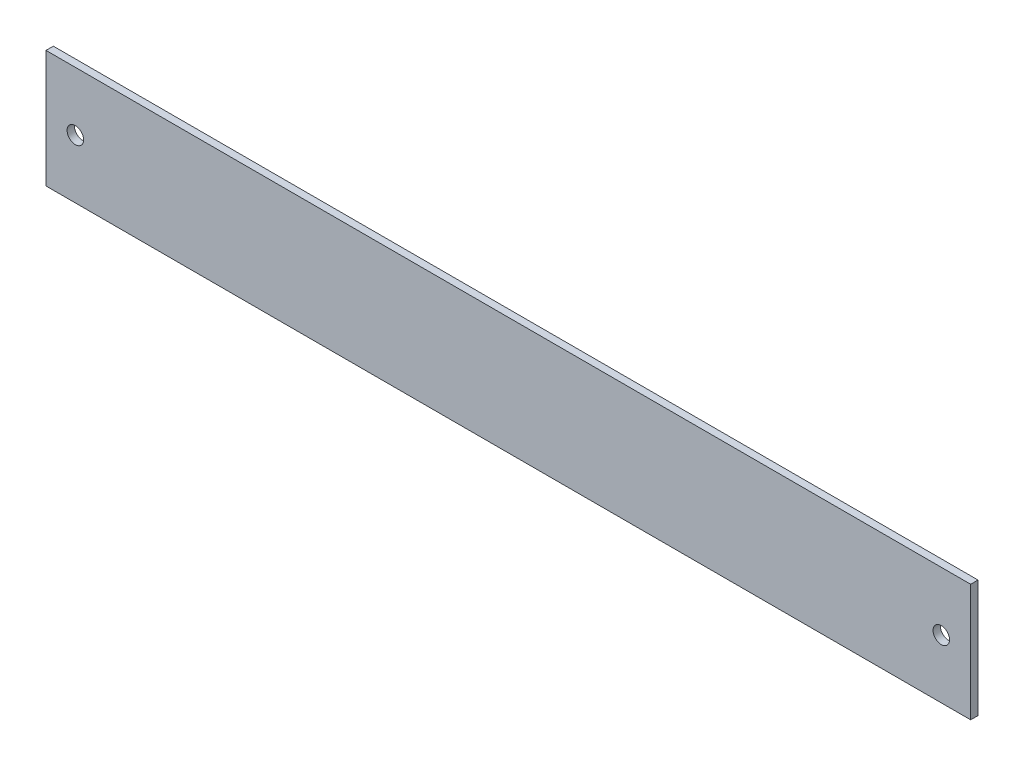
SolidWorks part; units mm, degrees
ref_plane "Front Plane" through (0, 0, 0) normal (0, 0, 1) x (1, 0, 0)
ref_plane "Top Plane" through (0, 0, 0) normal (0, 1, 0) x (1, 0, 0)
ref_plane "Right Plane" through (0, 0, 0) normal (1, 0, 0) x (0, 0, -1)
sketch "Sketch1" plane through (0, 0, 0) normal (0, 0, 1) x (1, 0, 0)
  line L1 (-200, -25.4) -> (200, -25.4)
  line L2 (-200, -25.4) -> (-200, 25.4)
  line L3 (-200, 25.4) -> (200, 25.4)
  line L4 (200, -25.4) -> (200, 25.4)
  line L5 (-200, -25.4) -> (200, 25.4) construction
  line L6 (-200, 25.4) -> (200, -25.4) construction
  point P0 (0, 0)
  dimension "D1" = 50.8
  dimension "D2" = 400
extrude "Boss-Extrude1" add sketch "Sketch1" along normal blind 3.175
sketch "Sketch2" plane through (0, 0, 3.175) normal (0, 0, 1) x (1, 0, 0)
  line L0 (-200, 25.4) -> (-200, -25.4) construction
  line L1 (200, -25.4) -> (200, 25.4) construction
  circle A0 centre (-187.3, 0) radius 3.5687
  circle A1 centre (187.3, 0) radius 3.5687
  point P8 (-187.3, 9.9532)
  dimension "D3" = 7.1374
  dimension "D1" = 12.7
  dimension "D2" = 12.7
extrude "Cut-Extrude1" cut sketch "Sketch2" against normal through all
